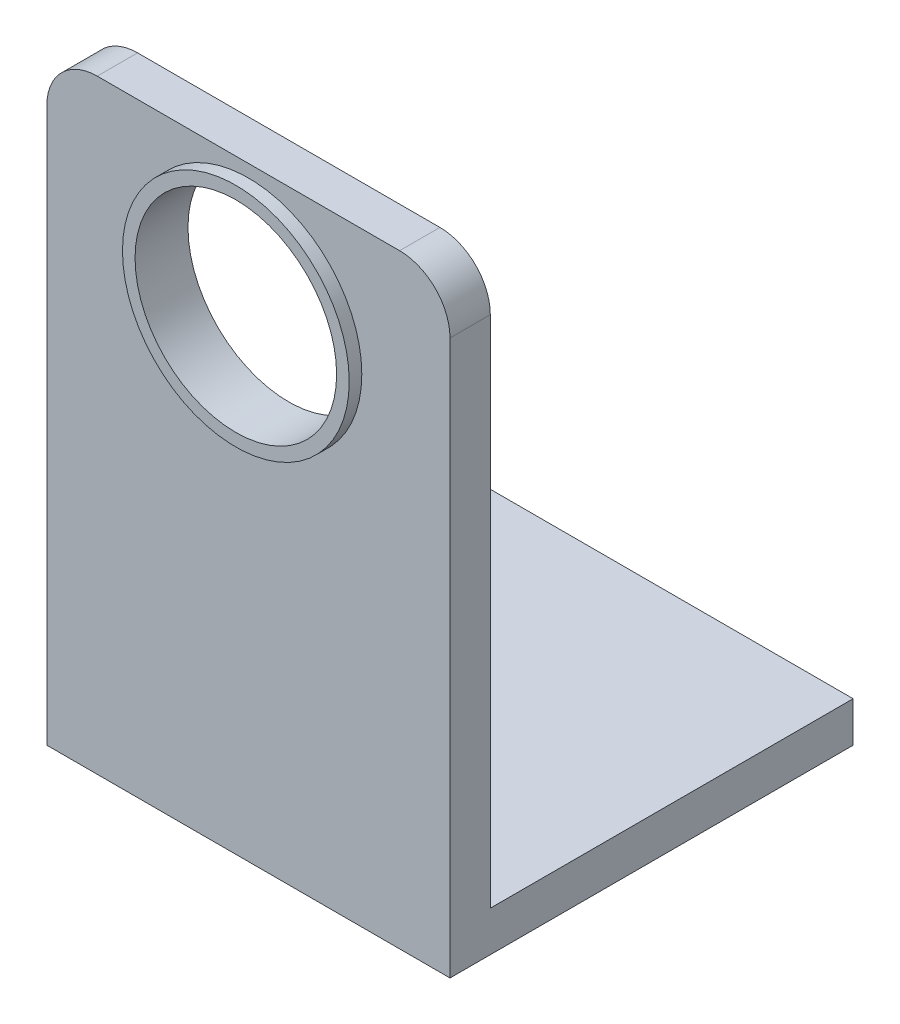
SolidWorks part; units mm, degrees
ref_plane "Front" through (0, 0, 0) normal (0, 0, 1) x (1, 0, 0)
ref_plane "Top" through (0, 0, 0) normal (0, 1, 0) x (1, 0, 0)
ref_plane "Right" through (0, 0, 0) normal (1, 0, 0) x (0, 0, -1)
sketch "Sketch1" plane through (0, 0, 0) normal (1, 0, 0) x (0, 0, -1)
  line L0 (2.54, 2.54) -> (25.4, 2.54)
  line L1 (0, 0) -> (25.4, 0)
  line L2 (0, 0) -> (0, 38.1)
  line L5 (2.54, 2.54) -> (2.54, 38.1)
  line L6 (25.4, 0) -> (25.4, 2.54)
  line L7 (0, 38.1) -> (2.54, 38.1)
  dimension "D1" = 38.1
  dimension "D2" = 2.54
  dimension "D3" = 25.4
extrude "Boss-Extrude1" add sketch "Sketch1" along normal blind 25.4
sketch "Sketch2" plane through (0, 0, -2.54) normal (0, 0, -1) x (-1, 0, 0)
  line L0 (-12.7, 38.1) -> (-12.7, 36.5125) construction
  line L1 (-25.4, 38.1) -> (0, 38.1) construction
  circle A0 centre (-12.7, 30.1625) radius 6.35
  dimension "D1" = 1.5875
  dimension "D2" = 12.7
extrude "Cut-Extrude1" cut sketch "Sketch2" against normal up to next
fillet "Fillet1" radius 3.175 2 edges at (0, 38.1, -1.27) (25.4, 38.1, -1.27)
sketch "Sketch3" plane through (0, 0, 0) normal (0, 0, 1) x (1, 0, 0)
  circle A0 centre (12.7, 30.1625) radius 6.35 construction
  circle A1 centre (12.7, 30.1625) radius 6.35
  circle A2 centre (12.7, 30.1625) radius 7.1438
  dimension "D1" = 0.7937
extrude "Boss-Extrude2" add sketch "Sketch3" along normal blind 0.7937
